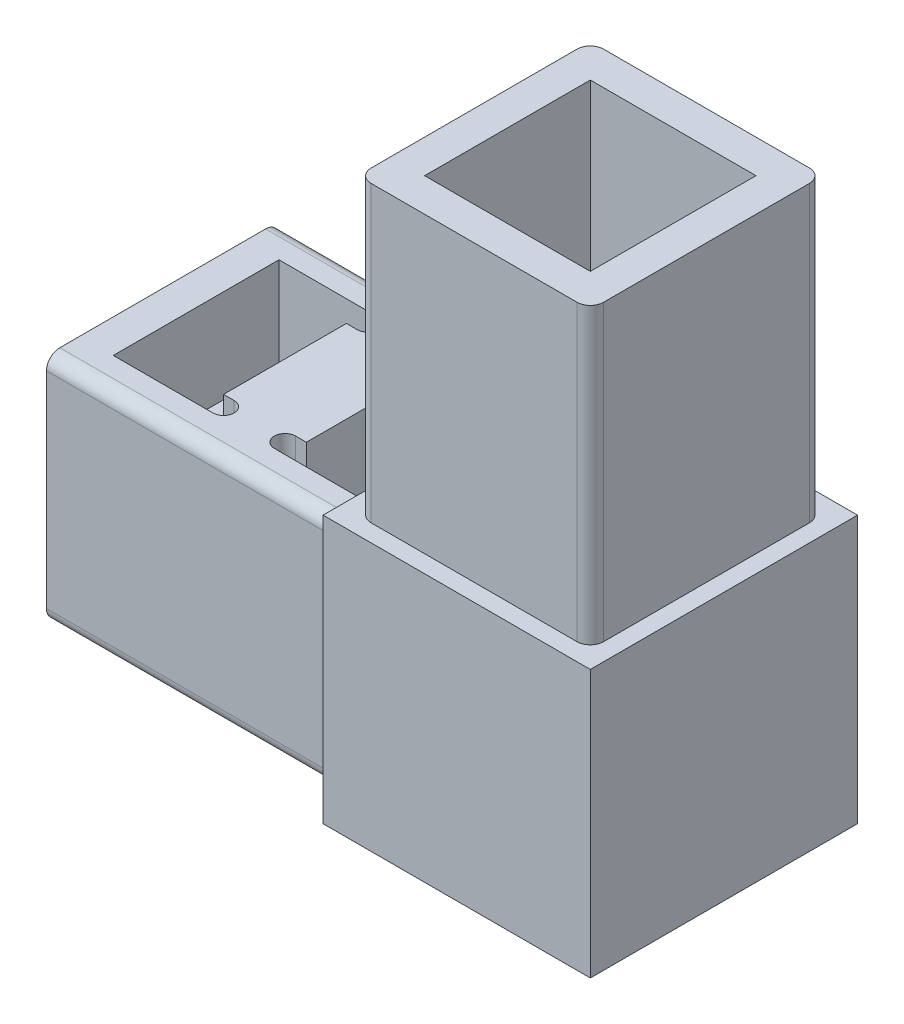
SolidWorks part; units mm, degrees
ref_plane "Front Plane" through (0, 0, 0) normal (0, 0, 1) x (1, 0, 0)
ref_plane "Top Plane" through (0, 0, 0) normal (0, 1, 0) x (1, 0, 0)
ref_plane "Right Plane" through (0, 0, 0) normal (1, 0, 0) x (0, 0, -1)
ref_plane "Plane1" through (0, 0, -12.7) normal (0, 0, -1) x (-1, 0, 0)
sketch "Sketch1" plane through (0, 0, -12.7) normal (0, 0, -1) x (-1, 0, 0)
  line L0 (12.7, 11.049) -> (-12.7, 11.049)
  line L1 (-12.7, 11.049) -> (-12.7, -11.049)
  line L2 (-12.7, -11.049) -> (12.7, -11.049)
  line L3 (12.7, -11.049) -> (12.7, 11.049)
extrude "Boss-Extrude1" add sketch "Sketch1" against normal blind 1.651
sketch "Sketch2" plane through (0, 0, -11.049) normal (0, 0, 1) x (1, 0, 0)
  line L0 (12.7, -11.049) -> (-40.64, -11.049)
  line L1 (-40.64, -11.049) -> (-40.64, 11.049)
  line L2 (-40.64, 11.049) -> (12.7, 11.049)
  line L3 (12.7, 11.049) -> (12.7, -11.049)
extrude "Boss-Extrude2" add sketch "Sketch2" along normal blind 22.098
sketch "Sketch3" plane through (0, 0, 11.049) normal (0, 0, 1) x (1, 0, 0)
  line L0 (-12.7, 11.049) -> (12.7, 11.049)
  line L1 (12.7, 11.049) -> (12.7, -11.049)
  line L2 (12.7, -11.049) -> (-12.7, -11.049)
  line L3 (-12.7, -11.049) -> (-12.7, 11.049)
extrude "Boss-Extrude3" add sketch "Sketch3" along normal blind 1.651
sketch "Sketch4" plane through (0, 11.049, 0) normal (0, 1, 0) x (-1, 0, 0)
  line L0 (12.7, -12.7) -> (-12.7, -12.7)
  line L1 (-12.7, -12.7) -> (-12.7, 12.7)
  line L2 (-12.7, 12.7) -> (12.7, 12.7)
  line L3 (12.7, 12.7) -> (12.7, -12.7)
extrude "Boss-Extrude4" add sketch "Sketch4" along normal blind 1.651
sketch "Sketch5" plane through (0, -11.049, 0) normal (0, -1, 0) x (1, 0, 0)
  line L0 (12.7, -12.7) -> (-12.7, -12.7)
  line L1 (-12.7, -12.7) -> (-12.7, 12.7)
  line L2 (-12.7, 12.7) -> (12.7, 12.7)
  line L3 (12.7, 12.7) -> (12.7, -12.7)
extrude "Boss-Extrude5" add sketch "Sketch5" along normal blind 1.651
sketch "Sketch6" plane through (0, 11.049, 0) normal (0, 1, 0) x (-1, 0, 0)
  line L0 (21.1455, 5.842) -> (22.1615, 5.842)
  line L1 (22.1615, 7.874) -> (12.7, 7.874)
  line L2 (12.7, 7.874) -> (12.7, -7.874)
  line L3 (12.7, -7.874) -> (22.1615, -7.874)
  line L4 (22.1615, -5.842) -> (21.1455, -5.842)
  line L5 (21.1455, -5.842) -> (21.1455, 5.842)
  arc A0 (22.1615, 5.842) -> (22.1615, 7.874) centre (22.1615, 6.858) ccw
  arc A1 (22.1615, -7.874) -> (22.1615, -5.842) centre (22.1615, -6.858) ccw
extrude "Cut-Extrude1" cut sketch "Sketch6" against normal blind 8.89
sketch "Sketch7" plane through (0, -11.049, 0) normal (0, -1, 0) x (1, 0, 0)
  line L0 (-22.1615, 5.842) -> (-21.1455, 5.842)
  line L1 (-21.1455, 5.842) -> (-21.1455, -5.842)
  line L2 (-21.1455, -5.842) -> (-22.1615, -5.842)
  line L3 (-22.1615, -7.874) -> (-12.7, -7.874)
  line L4 (-12.7, -7.874) -> (-12.7, 7.874)
  line L5 (-12.7, 7.874) -> (-22.1615, 7.874)
  arc A0 (-22.1615, -5.842) -> (-22.1615, -7.874) centre (-22.1615, -6.858) ccw
  arc A1 (-22.1615, 7.874) -> (-22.1615, 5.842) centre (-22.1615, 6.858) ccw
extrude "Cut-Extrude2" cut sketch "Sketch7" against normal blind 8.89
sketch "Sketch8" plane through (0, 11.049, 0) normal (0, 1, 0) x (-1, 0, 0)
  line L0 (28.0035, -7.874) -> (37.465, -7.874)
  line L1 (37.465, -7.874) -> (37.465, 7.874)
  line L2 (37.465, 7.874) -> (28.0035, 7.874)
  line L3 (28.0035, 5.842) -> (29.0195, 5.842)
  line L4 (29.0195, 5.842) -> (29.0195, -5.842)
  line L5 (29.0195, -5.842) -> (28.0035, -5.842)
  arc A0 (28.0035, -5.842) -> (28.0035, -7.874) centre (28.0035, -6.858) ccw
  arc A1 (28.0035, 7.874) -> (28.0035, 5.842) centre (28.0035, 6.858) ccw
extrude "Cut-Extrude3" cut sketch "Sketch8" against normal blind 8.89
sketch "Sketch9" plane through (0, -11.049, 0) normal (0, -1, 0) x (1, 0, 0)
  line L0 (-37.465, 7.874) -> (-37.465, -7.874)
  line L1 (-37.465, -7.874) -> (-28.0035, -7.874)
  line L2 (-28.0035, -5.842) -> (-29.0195, -5.842)
  line L3 (-29.0195, -5.842) -> (-29.0195, 5.842)
  line L4 (-29.0195, 5.842) -> (-28.0035, 5.842)
  line L5 (-28.0035, 7.874) -> (-37.465, 7.874)
  arc A0 (-28.0035, -7.874) -> (-28.0035, -5.842) centre (-28.0035, -6.858) ccw
  arc A1 (-28.0035, 5.842) -> (-28.0035, 7.874) centre (-28.0035, 6.858) ccw
extrude "Cut-Extrude4" cut sketch "Sketch9" against normal blind 8.89
sketch "Sketch10" plane through (0, 12.7, 0) normal (0, 1, 0) x (-1, 0, 0)
  line L0 (11.049, -11.049) -> (-11.049, -11.049)
  line L1 (-11.049, -11.049) -> (-11.049, 11.049)
  line L2 (-11.049, 11.049) -> (11.049, 11.049)
  line L3 (11.049, 11.049) -> (11.049, -11.049)
extrude "Boss-Extrude6" add sketch "Sketch10" along normal blind 27.94
sketch "Sketch11" plane through (0, 40.64, 0) normal (0, 1, 0) x (-1, 0, 0)
  line L0 (-7.874, -7.874) -> (7.874, -7.874)
  line L1 (7.874, -7.874) -> (7.874, 7.874)
  line L2 (7.874, 7.874) -> (-7.874, 7.874)
  line L3 (-7.874, 7.874) -> (-7.874, -7.874)
extrude "Cut-Extrude5" cut sketch "Sketch11" against normal blind 27.94
fillet "Fillet1" radius 1.27 8 edges at (-26.67, 11.049, 11.049) (-26.67, -11.049, -11.049) (-26.67, -11.049, 11.049) (-11.049, 26.67, -11.049) (-26.67, 11.049, -11.049) (11.049, 26.67, -11.049) (-11.049, 26.67, 11.049) (11.049, 26.67, 11.049)
